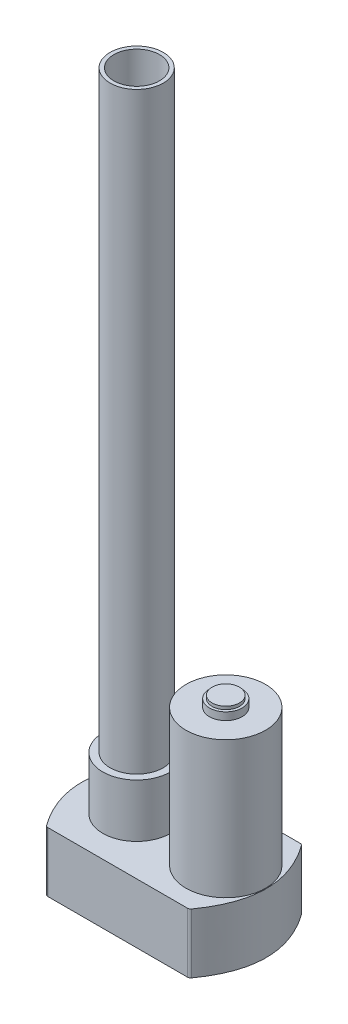
SolidWorks part; units mm, degrees
ref_plane "Front Plane" through (0, 0, 0) normal (0, 0, 1) x (1, 0, 0)
ref_plane "Top Plane" through (0, 0, 0) normal (0, 1, 0) x (1, 0, 0)
ref_plane "Right Plane" through (0, 0, 0) normal (1, 0, 0) x (0, 0, -1)
sketch "Sketch5" plane through (0, 0, 0) normal (0, 1, 0) x (1, 0, 0)
  line L2 (-52, -32) -> (42, -32)
  line L4 (-52, 42) -> (42, 42)
  spline S0 degree 2 poles (42, 42) (69.3, 5) (42, -32) knots 0 0 0 1 1 1
  spline S1 degree 2 poles (-52, 42) (-79.3, 5) (-52, -32) knots 0 0 0 1 1 1
  point P0 (0, 0)
  point P4 (1.6162, 5)
  point P11 (-44.4, 5)
  dimension "D1" = 94
  dimension "D2" = 74
extrude "Boss-Extrude3" add sketch "Sketch5" along normal blind 25 and the other way blind 14.3
sketch "Sketch6" plane through (0, 25, 0) normal (0, 1, 0) x (1, 0, 0)
  circle A1 centre (29.05, 5) radius 26.15
  point P0 (29.05, 5)
  dimension "D2" = 52.3
extrude "Boss-Extrude4" add sketch "Sketch6" along normal blind 90
sketch "Sketch7" plane through (0, 115, 0) normal (0, 1, 0) x (1, 0, 0)
  circle A0 centre (29.05, 5) radius 10.75
  circle A1 centre (29.05, 5) radius 8.15
  dimension "D1" = 21.5
  dimension "D2" = 16.3
extrude "Boss-Extrude5" add sketch "Sketch7" along normal blind 5
sketch "Sketch8" plane through (0, 115, 0) normal (0, 1, 0) x (1, 0, 0)
  circle A0 centre (29.05, 5) radius 9
  dimension "D1" = 18
extrude "Boss-Extrude6" add sketch "Sketch8" along normal blind 7
sketch "Sketch9" plane through (0, 25, 0) normal (0, 1, 0) x (1, 0, 0)
  line L0 (-51.8, 5) -> (-29.55, 5) construction
  line L1 (29.05, 5) -> (55.2, 5) construction
  circle A1 centre (-29.55, 5) radius 22.25
  circle A2 centre (-29.55, 5) radius 17.5
  circle A3 centre (29.05, 5) radius 26.15 construction
  circle A4 centre (29.05, 5) radius 26.15
  point P8 (-29.55, 5)
  dimension "D1" = 44.5
  dimension "D2" = 35
  dimension "D3" = 107
extrude "Boss-Extrude7" add sketch "Sketch9" along normal blind 35
sketch "Sketch10" plane through (0, 25, 0) normal (0, 1, 0) x (1, 0, 0)
  circle A0 centre (-29.55, 5) radius 17.5
  circle A1 centre (-29.55, 5) radius 15
  dimension "D1" = 35
  dimension "D2" = 30
extrude "Boss-Extrude8" add sketch "Sketch10" along normal blind 425
fillet "Fillet1" radius 2 4 edges at (42, 5.35, -42) (-52, 5.35, -42) (-52, 5.35, 32) (42, 5.35, 32)
ref_plane "Plane1" through (-29.55, 0, 0) normal (1, 0, 0) x (0, 0, -1)
